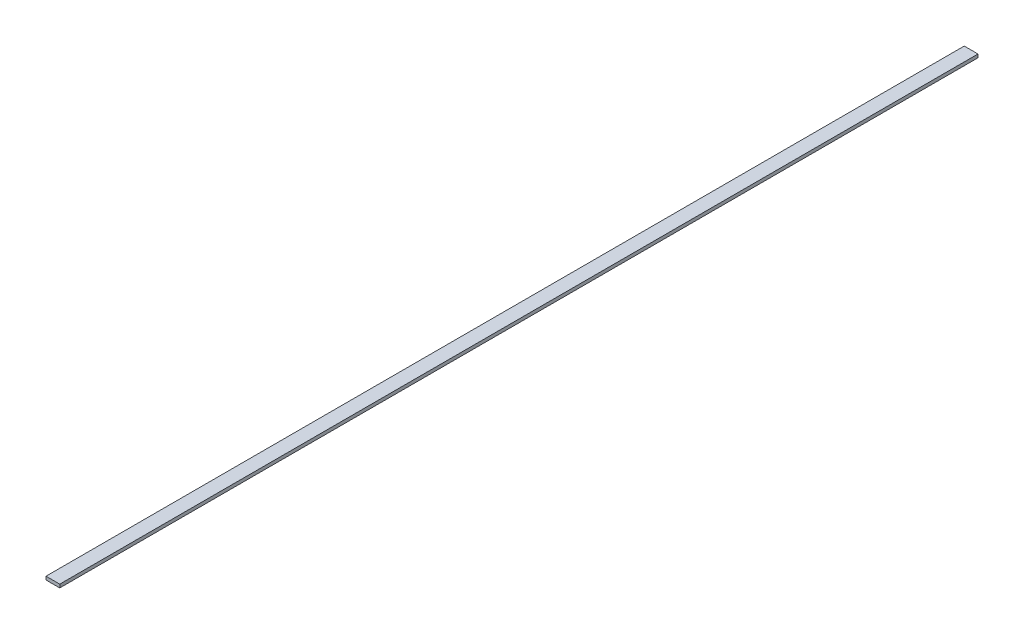
SolidWorks part; units mm, degrees
ref_plane "Alzado" through (0, 0, 0) normal (0, 0, 1) x (1, 0, 0)
ref_plane "Planta" through (0, 0, 0) normal (0, 1, 0) x (1, 0, 0)
ref_plane "Vista lateral" through (0, 0, 0) normal (1, 0, 0) x (0, 0, -1)
sketch "Croquis1" plane through (0, 0, 0) normal (0, 1, 0) x (1, 0, 0)
  line L1 (0, 0) -> (6.2, 0)
  line L2 (0, 0) -> (0, 414)
  line L3 (0, 414) -> (6.2, 414)
  line L4 (6.2, 0) -> (6.2, 414)
  dimension "D1" = 414
  dimension "D2" = 6.2
extrude "Saliente-Extruir1" add sketch "Croquis1" along normal blind 1.5
